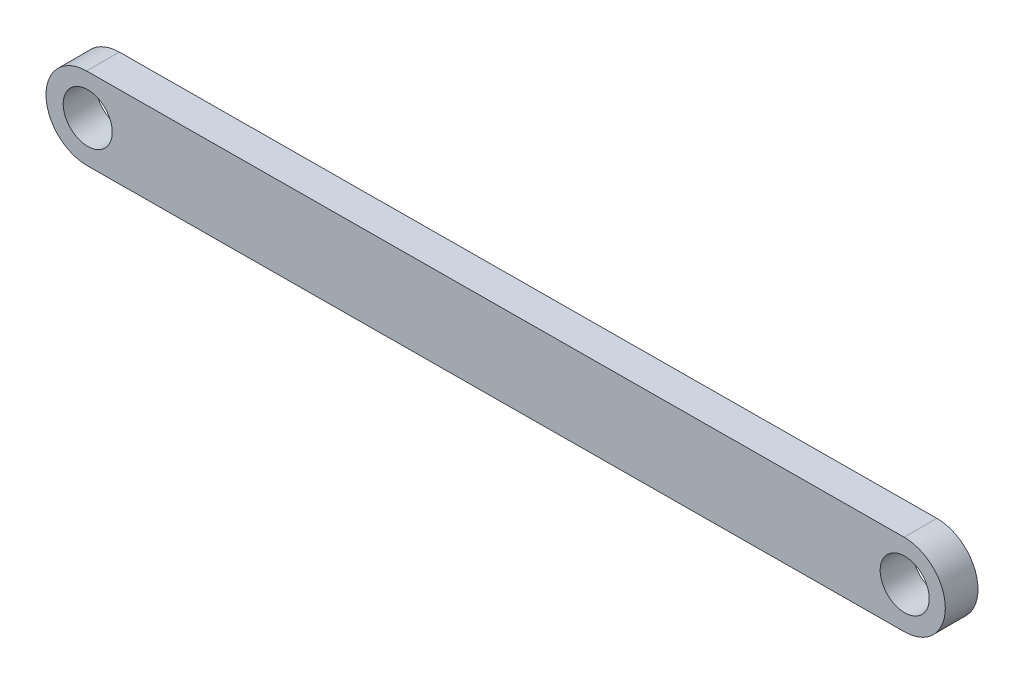
SolidWorks part; units mm, degrees
ref_plane "Front Plane" through (0, 0, 0) normal (0, 0, 1) x (1, 0, 0)
ref_plane "Top Plane" through (0, 0, 0) normal (0, 1, 0) x (1, 0, 0)
ref_plane "Right Plane" through (0, 0, 0) normal (1, 0, 0) x (0, 0, -1)
sketch "Sketch1" plane through (0, 0, 0) normal (0, 0, 1) x (1, 0, 0)
  line L0 (0.0255, -0.0638) -> (50.0255, 0.2404) construction
  line L1 (0.0103, 2.4361) -> (50.0103, 2.7404)
  line L2 (0.0407, -2.5638) -> (50.0407, -2.2595)
  arc A0 (0.0103, 2.4361) -> (0.0407, -2.5638) centre (0.0255, -0.0638) ccw
  arc A1 (50.0407, -2.2595) -> (50.0103, 2.7404) centre (50.0255, 0.2404) ccw
  circle A2 centre (0.077, -0.0231) radius 1.5
  circle A3 centre (50.0423, 0.2547) radius 1.5
  point P2 (25.0255, 0.0883)
  dimension "D3" = 3
  dimension "D4" = 3
  dimension "D1" = 50
  dimension "D2" = 5
extrude "Boss-Extrude1" add sketch "Sketch1" along normal blind 2
